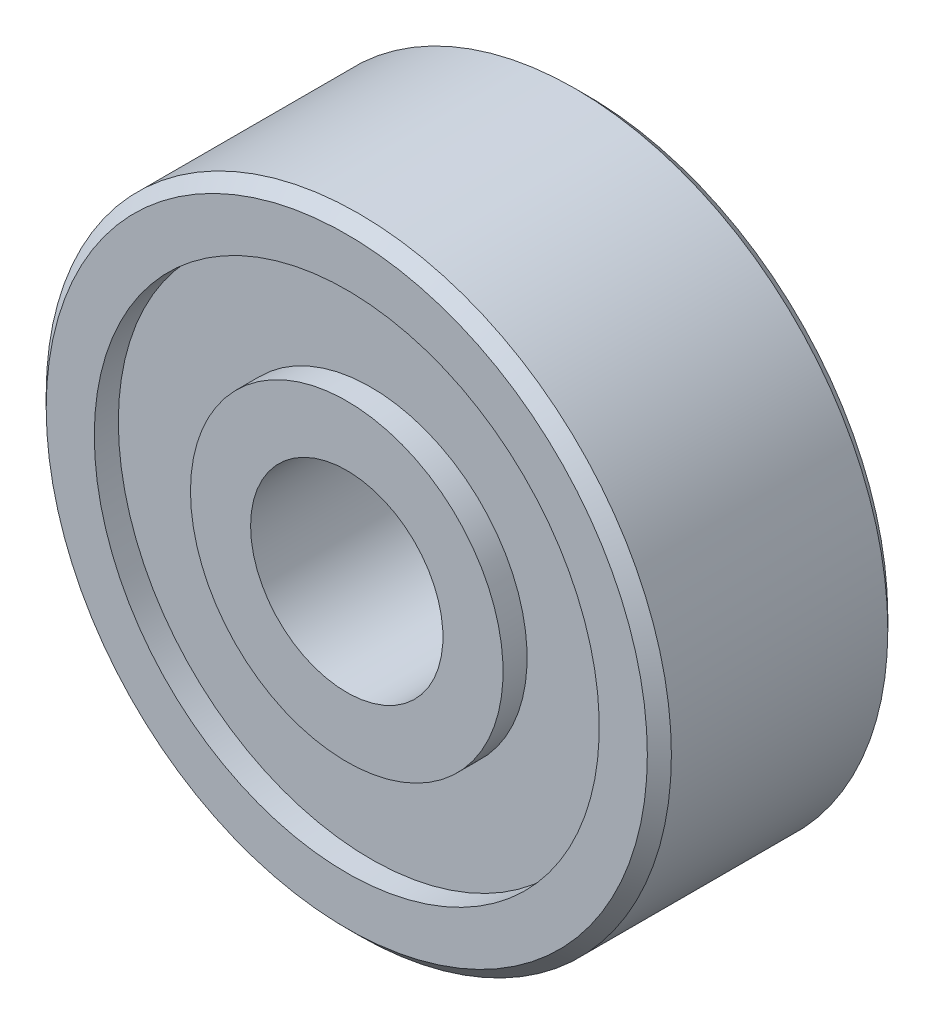
SolidWorks part; units mm, degrees
ref_plane "Front Plane" through (0, 0, 0) normal (0, 0, 1) x (1, 0, 0)
ref_plane "Top Plane" through (0, 0, 0) normal (0, 1, 0) x (1, 0, 0)
ref_plane "Right Plane" through (0, 0, 0) normal (1, 0, 0) x (0, 0, -1)
ref_plane "Plane1" through (0, 0, 0) normal (0, -1, 0) x (1, 0, 0)
sketch "Sketch1" plane through (0, 0, 0) normal (0, -1, 0) x (1, 0, 0)
  line L0 (6.5, 2.25) -> (6.25, 2.5)
  line L1 (6.25, 2.5) -> (5.25, 2.5)
  line L2 (5.25, 2.5) -> (5.25, 2)
  line L3 (5.25, 2) -> (3.25, 2)
  line L4 (3.25, 2) -> (3.25, 2.5)
  line L5 (3.25, 2.5) -> (2, 2.5)
  line L6 (2, 2.5) -> (2, -2.5)
  line L7 (2, -2.5) -> (3.25, -2.5)
  line L8 (3.25, -2.5) -> (3.25, -2)
  line L9 (3.25, -2) -> (5.25, -2)
  line L10 (5.25, -2) -> (5.25, -2.5)
  line L11 (5.25, -2.5) -> (6.25, -2.5)
  line L12 (6.25, -2.5) -> (6.5, -2.25)
  line L13 (6.5, -2.25) -> (6.5, 2.25)
  line L14 (0, 2.5) -> (0, -2.5) construction
revolve "Revolve1" add sketch "Sketch1" angle 360 about L14
